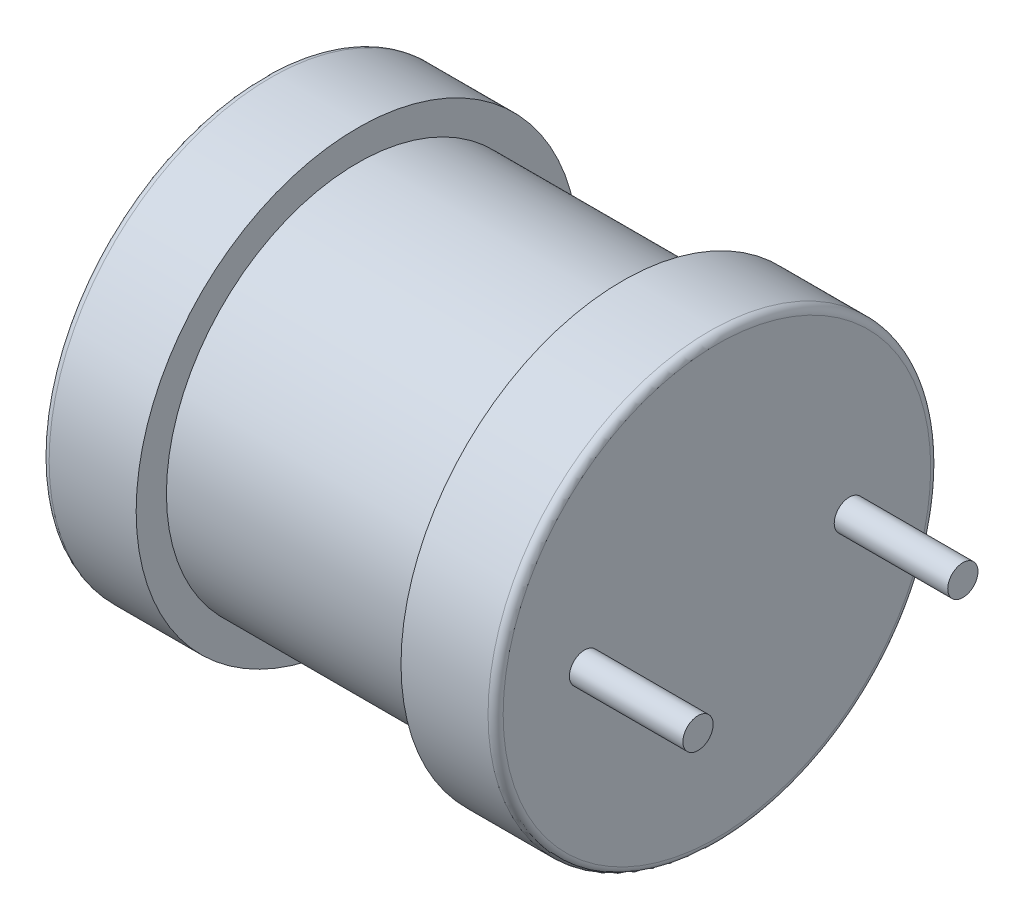
SolidWorks part; units mm, degrees
ref_plane "Спереди" through (0, 0, 0) normal (0, 0, 1) x (1, 0, 0)
ref_plane "Сверху" through (0, 0, 0) normal (0, 1, 0) x (1, 0, 0)
ref_plane "Справа" through (0, 0, 0) normal (1, 0, 0) x (0, 0, -1)
sketch "Эскиз1" plane through (0, 0, 0) normal (0, 0, 1) x (1, 0, 0)
  line L0 (-21.8885, 0) -> (26.367, 0) construction
  line L1 (0, 0) -> (0, 5.65)
  line L2 (0.2, 5.85) -> (2.5, 5.85)
  line L3 (2.5, 5.85) -> (2.5, 5.05)
  line L4 (2.5, 5.05) -> (9.5, 5.05)
  line L5 (9.5, 5.05) -> (9.5, 5.85)
  line L6 (9.5, 5.85) -> (11.8, 5.85)
  line L7 (12, 5.65) -> (12, 0)
  line L8 (12, 0) -> (0, 0)
  arc A0 (12, 5.65) -> (11.8, 5.85) centre (11.8, 5.65) ccw
  arc A1 (0, 5.65) -> (0.2, 5.85) centre (0.2, 5.65) cw
  point P13 (12, 5.85)
  point P16 (0, 5.85)
  dimension "D7" = 0.2
  dimension "D1" = 5.85
  dimension "D2" = 12
  dimension "D3" = 2.5
  dimension "D4" = 2.5
  dimension "D5" = 0.8
  dimension "D6" = 0.8
revolve "Повернуть1" add sketch "Эскиз1" angle 360 about L0
sketch "Эскиз2" plane through (12, 0, 0) normal (1, 0, 0) x (0, 0, -1)
  circle A0 centre (-3.5, 0) radius 0.4
  circle A1 centre (3.5, 0) radius 0.4
  dimension "D1" = 0.8
  dimension "D2" = 3.5
  dimension "D3" = 2
extrude "Бобышка-Вытянуть2" add sketch "Эскиз2" along normal blind 3 contours A1 | A0
sketch "Эскиз4" plane through (0, 0, 0) normal (-1, 0, 0) x (0, 0, 1)
  text T0 "RLB1314" font "Arial" height in points 6
extrude "Вырез-Вытянуть1" cut sketch "Эскиз4" against normal blind 0.2
